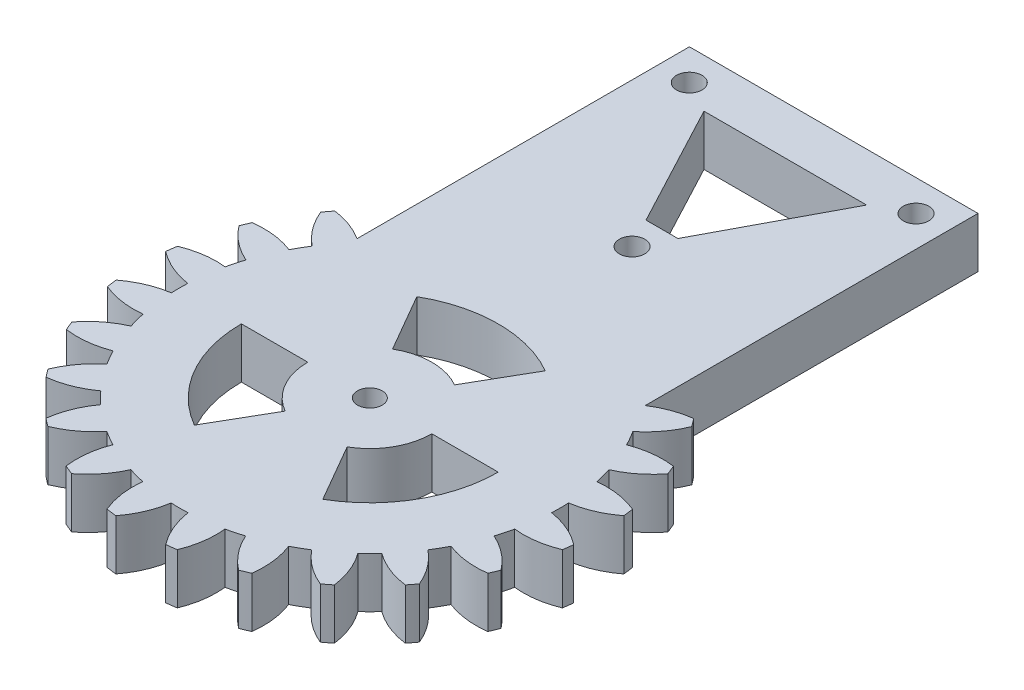
SolidWorks part; units mm, degrees
ref_plane "Front Plane" through (0, 0, 0) normal (0, 0, 1) x (1, 0, 0)
ref_plane "Top Plane" through (0, 0, 0) normal (0, 1, 0) x (1, 0, 0)
ref_plane "Right Plane" through (0, 0, 0) normal (1, 0, 0) x (0, 0, -1)
sketch "Sketch1" plane through (0, 0, 0) normal (0, 1, 0) x (1, 0, 0)
  line L1 (-16.2947, -55.4739) -> (16.2826, -55.4739)
  line L2 (-16.2947, -92.9976) -> (-16.2947, -55.4739)
  line L3 (3.5013, -113.9088) -> (7.2508, -120.4032)
  line L4 (16.2826, -93.0436) -> (16.2826, -55.4739)
  line L7 (-9.2395, -62.491) -> (-9.2962, -62.491)
  line L8 (-9.18, -60.9458) -> (9.18, -60.9458)
  line L9 (9.18, -60.9458) -> (1.8, -74.8677)
  line L10 (-9.18, -60.9458) -> (-1.8, -74.8677)
  line L11 (-1.8, -74.8677) -> (1.8, -74.8677)
  line L15 (-3.4987, -113.9088) -> (-7.2482, -120.4032)
  line L16 (-9.2962, -62.491) -> (-9.2395, -62.491)
  line L17 (-6.9987, -107.8467) -> (-14.4977, -107.8467)
  line L20 (7.0013, -107.8467) -> (14.5003, -107.8467)
  line L22 (3.5013, -101.7845) -> (7.2502, -95.2898)
  line L23 (-3.4987, -101.7845) -> (-7.2482, -95.2902)
  circle A0 centre (0, -78.2429) radius 1.44
  circle A1 centre (-12.8, -58.9858) radius 1.44
  circle A2 centre (12.8, -58.9858) radius 1.44
  arc A3 (-6.9987, -107.8467) -> (-3.4987, -113.9088) centre (0.0013, -107.8467) ccw
  arc A4 (-14.4977, -107.8467) -> (-7.2482, -120.4032) centre (0.0013, -107.8467) ccw
  arc A5 (3.5013, -113.9088) -> (7.0013, -107.8467) centre (0.0013, -107.8467) ccw
  arc A6 (7.2508, -120.4032) -> (14.5003, -107.8467) centre (0.0013, -107.8467) ccw
  arc A7 (3.5034, -101.7857) -> (-3.4987, -101.7845) centre (0.0013, -107.8467) ccw
  arc A8 (-14.4977, -107.8467) -> (-7.2482, -120.4032) centre (0.0013, -107.8467) ccw
  arc A9 (7.2502, -95.2898) -> (-7.2482, -95.2902) centre (0.0013, -107.8467) ccw
  arc A10 (7.2508, -120.4032) -> (14.5003, -107.8467) centre (0.0013, -107.8467) ccw
  arc A19 (-16.2947, -92.9976) -> (-20.2497, -91.5435) centre (-21.5044, -101.0611) ccw
  arc A20 (-20.2497, -91.5435) -> (-20.9448, -92.4467) centre (0.0013, -107.8467) ccw
  arc A21 (-20.9448, -92.4467) -> (-18.105, -96.2587) centre (-12.0659, -88.7962) ccw
  arc A22 (-18.105, -96.2587) -> (-19.061, -97.9094) centre (0.0013, -107.8467) ccw
  arc A23 (-19.061, -97.9094) -> (-23.7806, -97.3436) centre (-22.5279, -106.8615) ccw
  arc A24 (-23.7806, -97.3436) -> (-24.2194, -98.3993) centre (0.0013, -107.8467) ccw
  arc A25 (-24.2194, -98.3993) -> (-20.489, -101.3454) centre (-16.5896, -92.5731) ccw
  arc A26 (-20.489, -101.3454) -> (-20.986, -103.1932) centre (0.0013, -107.8467) ccw
  arc A27 (-20.986, -103.1932) -> (-25.6909, -103.8708) centre (-22.0125, -112.7381) ccw
  arc A28 (-25.6909, -103.8708) -> (-25.8458, -105.0497) centre (0.0013, -107.8467) ccw
  arc A29 (-25.8458, -105.0497) -> (-21.478, -106.9251) centre (-19.9922, -97.4408) ccw
  arc A30 (-21.478, -106.9251) -> (-21.478, -108.7682) centre (0.0013, -107.8467) ccw
  arc A31 (-21.478, -108.7682) -> (-25.8485, -110.6373) centre (-20.006, -118.2547) ccw
  arc A32 (-25.8485, -110.6373) -> (-25.7015, -111.7665) centre (0.0013, -107.8467) ccw
  arc A33 (-25.7015, -111.7665) -> (-20.9981, -112.4544) centre (-22.0038, -102.9073) ccw
  arc A34 (-20.9981, -112.4544) -> (-20.5075, -114.2962) centre (0.0013, -107.8467) ccw
  arc A35 (-20.5075, -114.2962) -> (-24.2454, -117.2327) centre (-16.6304, -123.0784) ccw
  arc A36 (-24.2454, -117.2327) -> (-23.8111, -118.2856) centre (0.0013, -107.8467) ccw
  arc A37 (-23.8111, -118.2856) -> (-19.0899, -117.7327) centre (-22.5324, -108.7712) ccw
  arc A38 (-19.0899, -117.7327) -> (-18.1391, -119.3849) centre (0.0013, -107.8467) ccw
  arc A39 (-18.1391, -119.3849) -> (-20.9895, -123.189) centre (-12.121, -126.8643) ccw
  arc A40 (-20.9895, -123.189) -> (-20.297, -124.0941) centre (0.0013, -107.8467) ccw
  arc A41 (-20.297, -124.0941) -> (-15.8799, -122.3378) centre (-21.5249, -114.5729) ccw
  arc A42 (-15.8799, -122.3378) -> (-14.5331, -123.6883) centre (0.0013, -107.8467) ccw
  arc A43 (-14.5331, -123.6883) -> (-16.3014, -128.1006) centre (-6.7836, -129.3545) ccw
  arc A44 (-16.3014, -128.1006) -> (-15.396, -128.7972) centre (0.0013, -107.8467) ccw
  arc A45 (-15.396, -128.7972) -> (-11.5845, -125.9568) centre (-19.0481, -119.919) ccw
  arc A46 (-11.5845, -125.9568) -> (-9.93, -126.9143) centre (0.0013, -107.8467) ccw
  arc A47 (-9.93, -126.9143) -> (-10.4941, -131.6342) centre (-0.9767, -130.3781) ccw
  arc A48 (-10.4941, -131.6342) -> (-9.4294, -132.076) centre (0.0013, -107.8467) ccw
  arc A49 (-9.4294, -132.076) -> (-6.486, -128.3436) centre (-15.2611, -124.4503) ccw
  arc A50 (-6.486, -128.3436) -> (-4.6452, -128.8375) centre (0.0013, -107.8467) ccw
  arc A51 (-4.6452, -128.8375) -> (-3.9798, -133.5401) centre (4.8974, -129.8856) ccw
  arc A52 (-3.9798, -133.5401) -> (-2.8271, -133.6924) centre (0.0013, -107.8467) ccw
  arc A53 (-2.8271, -133.6924) -> (-0.9516, -129.3245) centre (-10.436, -127.8388) ccw
  arc A54 (-0.9516, -129.3245) -> (0.9542, -129.3245) centre (0.0013, -107.8467) ccw
  arc A55 (0.9542, -129.3245) -> (2.8058, -133.695) centre (10.4451, -127.8812) ccw
  arc A56 (2.8058, -133.695) -> (3.9587, -133.5437) centre (0.0013, -107.8467) ccw
  arc A57 (3.9587, -133.5437) -> (4.6397, -128.8393) centre (-4.906, -129.8589) ccw
  arc A58 (4.6397, -128.8393) -> (6.4806, -128.3461) centre (0.0013, -107.8467) ccw
  arc A59 (6.4806, -128.3461) -> (9.4226, -132.0797) centre (15.2572, -124.4562) ccw
  arc A60 (9.4226, -132.0797) -> (10.4747, -131.6439) centre (0.0013, -107.8467) ccw
  arc A61 (10.4747, -131.6439) -> (9.915, -126.9235) centre (0.9584, -130.379) ccw
  arc A62 (9.915, -126.9235) -> (11.5655, -125.9706) centre (0.0013, -107.8467) ccw
  arc A63 (11.5655, -125.9706) -> (15.3736, -128.8155) centre (19.0363, -119.9417) ccw
  arc A64 (15.3736, -128.8155) -> (16.277, -128.1223) centre (0.0013, -107.8467) ccw
  arc A65 (16.277, -128.1223) -> (14.5146, -123.7076) centre (6.7576, -129.3635) ccw
  arc A66 (14.5146, -123.7076) -> (15.8623, -122.36) centre (0.0013, -107.8467) ccw
  arc A67 (15.8623, -122.36) -> (20.2769, -124.1224) centre (21.5181, -114.603) ccw
  arc A68 (20.2769, -124.1224) -> (20.9701, -123.2189) centre (0.0013, -107.8467) ccw
  arc A69 (20.9701, -123.2189) -> (18.1252, -119.4109) centre (12.0963, -126.8817) ccw
  arc A70 (18.1252, -119.4109) -> (19.0781, -117.7603) centre (0.0013, -107.8467) ccw
  arc A71 (19.0781, -117.7603) -> (23.7985, -118.3201) centre (22.5336, -108.8038) ccw
  arc A72 (23.7985, -118.3201) -> (24.2343, -117.268) centre (0.0013, -107.8467) ccw
  arc A73 (24.2343, -117.268) -> (20.5007, -114.326) centre (16.6108, -123.1026) ccw
  arc A74 (20.5007, -114.326) -> (20.994, -112.4851) centre (0.0013, -107.8467) ccw
  arc A75 (20.994, -112.4851) -> (25.6984, -111.804) centre (22.0135, -102.9394) ccw
  arc A76 (25.6984, -111.804) -> (25.847, -110.675) centre (0.0013, -107.8467) ccw
  arc A77 (25.847, -110.675) -> (21.4792, -108.7996) centre (19.9934, -118.2839) ccw
  arc A78 (21.4792, -108.7996) -> (21.4792, -106.8937) centre (0.0013, -107.8467) ccw
  arc A79 (21.4792, -106.8937) -> (25.847, -105.0183) centre (19.9934, -97.4094) ccw
  arc A80 (25.847, -105.0183) -> (25.6984, -103.8893) centre (0.0013, -107.8467) ccw
  arc A81 (25.6984, -103.8893) -> (20.994, -103.2082) centre (22.0135, -112.7539) ccw
  arc A82 (20.994, -103.2082) -> (20.5007, -101.3673) centre (0.0013, -107.8467) ccw
  arc A83 (20.5007, -101.3673) -> (24.2343, -98.4253) centre (16.6108, -92.5907) ccw
  arc A84 (24.2343, -98.4253) -> (23.7985, -97.3732) centre (0.0013, -107.8467) ccw
  arc A85 (23.7985, -97.3732) -> (19.0781, -97.933) centre (22.5336, -106.8895) ccw
  arc A86 (19.0781, -97.933) -> (18.1252, -96.2825) centre (0.0013, -107.8467) ccw
  arc A87 (18.1252, -96.2825) -> (20.9701, -92.4744) centre (12.0963, -88.8117) ccw
  arc A88 (20.9701, -92.4744) -> (20.2769, -91.5709) centre (0.0013, -107.8467) ccw
  arc A89 (20.2769, -91.5709) -> (16.2826, -93.0436) centre (21.5181, -101.0904) ccw
  circle A97 centre (0.0013, -107.8467) radius 1.4
  dimension "D3" = 3.3752
  dimension "D2" = 1.96
  dimension "D1" = 14
  dimension "D4" = 3.62
  dimension "D5" = 3.62
  dimension "D6" = 1.8
  dimension "D7" = 1.8
  dimension "D8" = 12.8
  dimension "D9" = 12.8
extrude "Boss-Extrude2" add sketch "Sketch1" along normal blind 5.7 contours A88 A89 L4 L1 L2 A19 A20 A21 A22 A23 A24 A25 A26 A27 A28 A29 A30 A31 A32 A33 A34 A35 A36 A37 A38 A39 A40 A41 A42 A43 A44 A45 A46 A47 A48 A49 A50 A51 A52 A53 A54 A55 A56 A57 A58 A59 A60 A61 A62 A63 A64
